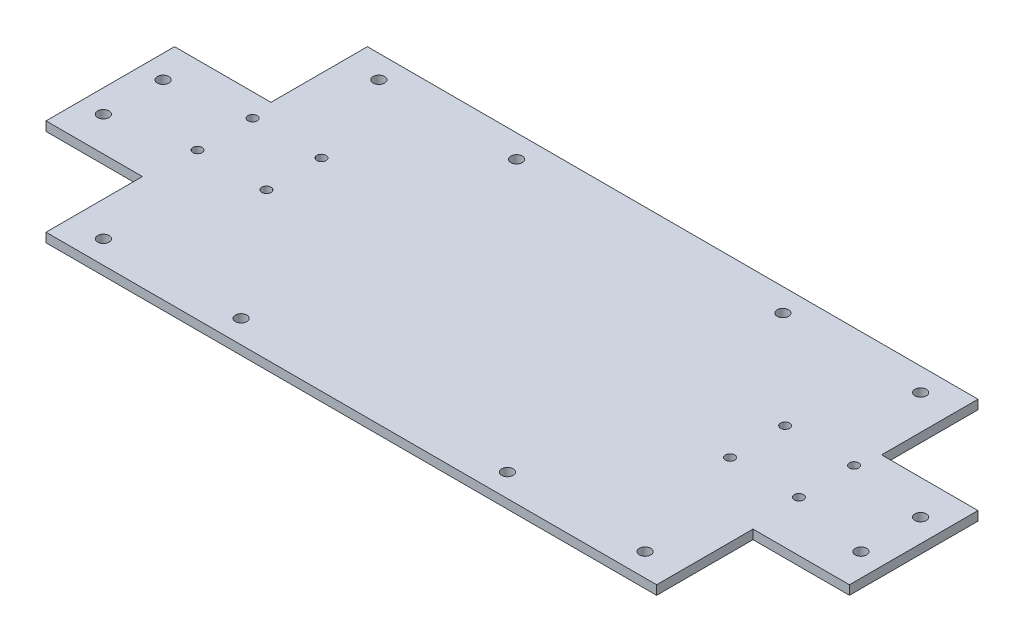
SolidWorks part; units mm, degrees
ref_plane "Front Plane" through (0, 0, 0) normal (0, 0, 1) x (1, 0, 0)
ref_plane "Top Plane" through (0, 0, 0) normal (0, 1, 0) x (1, 0, 0)
ref_plane "Right Plane" through (0, 0, 0) normal (1, 0, 0) x (0, 0, -1)
sketch "Sketch1" plane through (0, 0, 0) normal (0, 1, 0) x (1, 0, 0)
  line L1 (175, -70) -> (-175, -70)
  line L2 (175, -70) -> (175, 70)
  line L3 (175, 70) -> (-175, 70)
  line L4 (-175, -70) -> (-175, 70)
  line L5 (175, -70) -> (-175, 70) construction
  line L6 (175, 70) -> (-175, -70) construction
  point P0 (0, 0)
  dimension "D1" = 350
  dimension "D2" = 140
extrude "Boss-Extrude1" add sketch "Sketch1" along normal blind 4
sketch "Sketch2" plane through (0, 4, 0) normal (0, 1, 0) x (1, 0, 0)
  line L0 (0, 0) -> (0, 95.3674) construction
  line L1 (-175, -70) -> (-133, -70)
  line L2 (-175, -70) -> (-175, -28)
  line L3 (-175, -28) -> (-133, -28)
  line L4 (-133, -70) -> (-133, -28)
  line L5 (133, -70) -> (133, -28)
  line L6 (175, -70) -> (133, -70)
  line L7 (175, -70) -> (175, -28)
  line L8 (175, -28) -> (133, -28)
  line L9 (0, 0) -> (203.1909, 0) construction
  line L10 (175, 70) -> (133, 70)
  line L11 (175, 70) -> (175, 28)
  line L12 (175, 28) -> (133, 28)
  line L13 (133, 70) -> (133, 28)
  line L14 (-133, 70) -> (-133, 28)
  line L15 (-175, 70) -> (-133, 70)
  line L16 (-175, 70) -> (-175, 28)
  line L17 (-175, 28) -> (-133, 28)
  line L18 (-175, 70) -> (-175, -70) construction
  line L19 (175, 70) -> (-175, 70) construction
  circle A0 centre (-165, 13) radius 2.5
  circle A1 centre (-165, -13) radius 2.5
  circle A2 centre (165, -13) radius 2.5
  circle A3 centre (165, 13) radius 2.5
  circle A4 centre (-118, 60) radius 2.5
  circle A5 centre (-58, 60) radius 2.5
  circle A6 centre (58, 60) radius 2.5
  circle A7 centre (118, 60) radius 2.5
  circle A8 centre (118, -60) radius 2.5
  circle A9 centre (58, -60) radius 2.5
  circle A10 centre (-58, -60) radius 2.5
  circle A11 centre (-118, -60) radius 2.5
  dimension "D3" = 10
  dimension "D5" = 5
  dimension "D6" = 10
  dimension "D8" = 60
  dimension "D9" = 5
  dimension "D10" = 5
  dimension "D1" = 42
  dimension "D2" = 42
  dimension "D4" = 15
  dimension "D7" = 15
  dimension "D11" = 10
extrude "Cut-Extrude1" cut sketch "Sketch2" against normal through all
sketch "Sketch3" plane through (0, 4, 0) normal (0, 1, 0) x (1, 0, 0)
  line L0 (133, 70) -> (-133, 70) construction
  line L1 (-175, 28) -> (-175, -28) construction
  line L2 (0, 70) -> (0, -101.5955) construction
  line L4 (-133, -70) -> (133, -70) construction
  circle A0 centre (-131, 18) radius 2
  circle A1 centre (-131, -6) radius 2
  circle A2 centre (131, -6) radius 2
  circle A3 centre (131, 18) radius 2
  circle A4 centre (-101, 18) radius 2
  circle A5 centre (-101, -6) radius 2
  circle A6 centre (101, -6) radius 2
  circle A7 centre (101, 18) radius 2
  dimension "D1" = 4
  dimension "D3" = 4
  dimension "D7" = 30
  dimension "D9" = 4
  dimension "D10" = 4
  dimension "D11" = 52
  dimension "D12" = 64
  dimension "D2" = 52
  dimension "D4" = 44
  dimension "D5" = 44
  dimension "D6" = 24
  dimension "D8" = 30
extrude "Cut-Extrude2" cut sketch "Sketch3" against normal blind 10 contours A1 | A5 | A4 | A6 | A0 | A7 | A3 | A2
